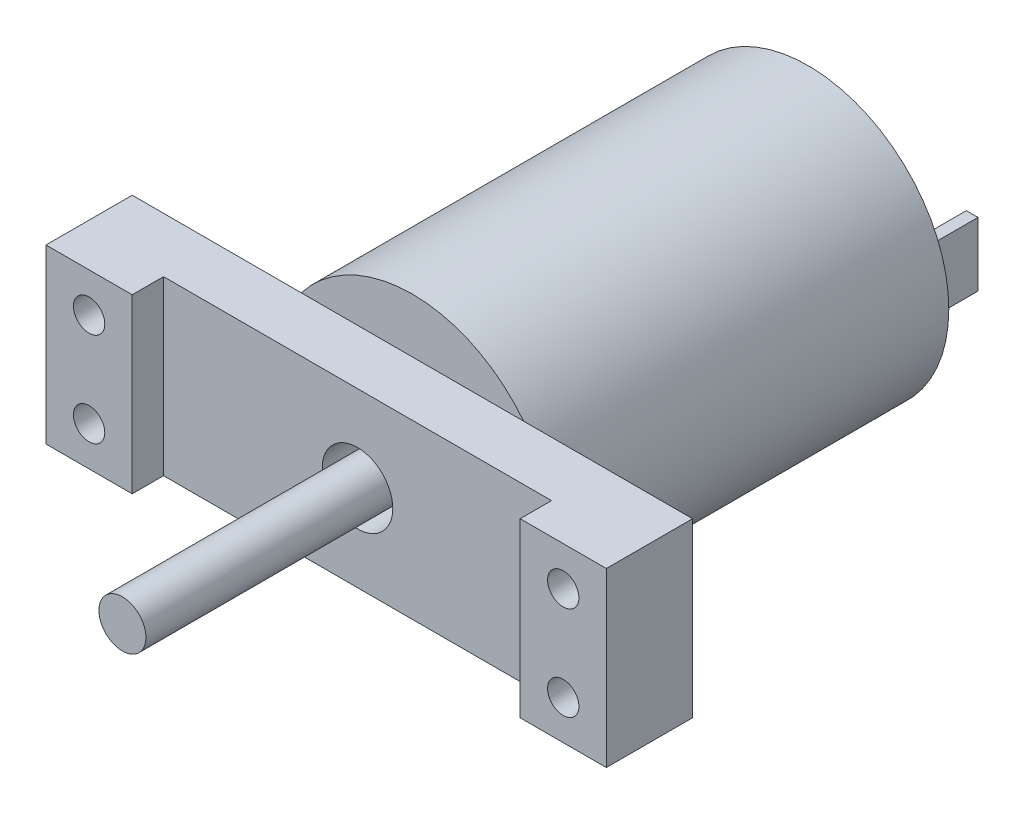
SolidWorks part; units mm, degrees
ref_plane "Front Plane" through (0, 0, 0) normal (0, 0, 1) x (1, 0, 0)
ref_plane "Top Plane" through (0, 0, 0) normal (0, 1, 0) x (1, 0, 0)
ref_plane "Right Plane" through (0, 0, 0) normal (1, 0, 0) x (0, 0, -1)
sketch "Sketch1" plane through (0, 0, 0) normal (0, 0, 1) x (1, 0, 0)
  circle A0 centre (0, 0) radius 17.95
extrude "Boss-Extrude1" add sketch "Sketch1" along normal blind 50.5
sketch "Sketch2" plane through (0, 0, 50.5) normal (0, 0, 1) x (1, 0, 0)
  circle A0 centre (0, 0) radius 3
extrude "Boss-Extrude2" add sketch "Sketch2" along normal blind 37
sketch "Sketch3" plane through (0, 0, 50.5) normal (0, 0, 1) x (1, 0, 0)
  line L3 (-35.75, -11) -> (35.75, -11)
  line L4 (-35.75, -11) -> (-35.75, 11)
  line L5 (-35.75, 11) -> (35.75, 11)
  line L6 (35.75, -11) -> (35.75, 11)
  circle A0 centre (0, 0) radius 4.5
  point P4 (0, 0)
  point P9 (0, 0)
extrude "Boss-Extrude3" add sketch "Sketch3" along normal blind 7
sketch "Sketch4" plane through (0, 0, 57.5) normal (0, 0, 1) x (1, 0, 0)
  line L0 (-35.75, -11) -> (35.75, -11) construction
  line L1 (-35.75, 11) -> (-24.75, 11)
  line L2 (-35.75, 11) -> (-35.75, -11)
  line L3 (-35.75, -11) -> (-24.75, -11)
  line L4 (-24.75, 11) -> (-24.75, -11)
  line L6 (35.75, 11) -> (24.75, 11)
  line L7 (35.75, 11) -> (35.75, -11)
  line L8 (35.75, -11) -> (24.75, -11)
  line L9 (24.75, 11) -> (24.75, -11)
extrude "Boss-Extrude4" add sketch "Sketch4" along normal blind 4
sketch "Sketch5" plane through (0, 0, 61.5) normal (0, 0, 1) x (1, 0, 0)
  circle A0 centre (-30.25, 6) radius 2
  circle A1 centre (-30.25, -6) radius 2
  circle A2 centre (30.25, -6) radius 2
  circle A3 centre (30.25, 6) radius 2
extrude "Cut-Extrude1" cut sketch "Sketch5" against normal up to surface (11 mm away) up to face at (-25.9086, 0, 50.5)
sketch "Sketch6" plane through (0, 0, 0) normal (0, 0, -1) x (-1, 0, 0)
  line L1 (-14.6746, 5.0101) -> (-13.1878, 5.0101)
  line L2 (-14.6746, 5.0101) -> (-14.6746, -3.1353)
  line L3 (-14.6746, -3.1353) -> (-13.1878, -3.1353)
  line L4 (-13.1878, 5.0101) -> (-13.1878, -3.1353)
  line L5 (12.1534, 5.0101) -> (14.0282, 5.0101)
  line L6 (12.1534, 5.0101) -> (12.1534, -3.1353)
  line L7 (12.1534, -3.1353) -> (14.0282, -3.1353)
  line L8 (14.0282, 5.0101) -> (14.0282, -3.1353)
extrude "Boss-Extrude6" add sketch "Sketch6" along normal blind 7
